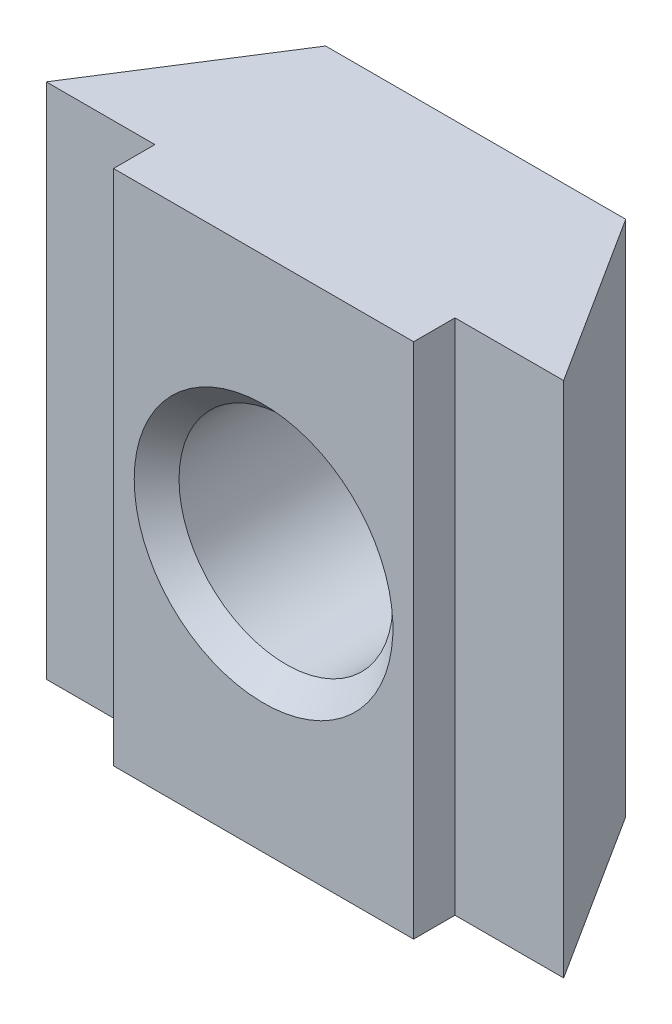
SolidWorks part; units mm, degrees
ref_plane "Piano frontale" through (0, 0, 0) normal (0, 0, 1) x (1, 0, 0)
ref_plane "Piano superiore" through (0, 0, 0) normal (0, 1, 0) x (1, 0, 0)
ref_plane "Piano destro" through (0, 0, 0) normal (1, 0, 0) x (0, 0, -1)
ref_plane "Plane1" through (0, 23.4, 0) normal (0, -1, 0) x (1, 0, 0)
sketch "Sketch1" plane through (0, 23.4, 0) normal (0, -1, 0) x (1, 0, 0)
  line L0 (-13.1, -10.8) -> (-11, -7.5)
  line L1 (-11, -7.5) -> (-21, -7.5)
  line L2 (-21, -7.5) -> (-18.9, -10.8)
  line L3 (-18.9, -10.8) -> (-13.1, -10.8)
extrude "Extrude1" add sketch "Sketch1" against normal blind 10
sketch "Sketch2" plane through (0, 0, -7.5) normal (0, 0, 1) x (1, 0, 0)
  line L0 (-18.9, 33.4) -> (-13.1, 33.4)
  line L1 (-13.1, 33.4) -> (-13.1, 23.4)
  line L2 (-13.1, 23.4) -> (-18.9, 23.4)
  line L3 (-18.9, 23.4) -> (-18.9, 33.4)
extrude "Extrude2" add sketch "Sketch2" along normal blind 0.8
hole_wizard "HoleWzd1" positions "Sketch4" profile "Sketch3" hole size "M3.5" standard "Ansi Metric"
sketch "Sketch4" plane through (0, 0, -6.7) normal (0, 0, 1) x (1, 0, 0)
  point P0 (-16, 28.4)
sketch "Sketch3" plane through (-16, 28.4, -6.7) normal (1, 0, 0) x (0, -1, 0)
  line L0 (0, 0) -> (0, 4.1)
  line L1 (0, 4.1) -> (2.067, 4.1)
  line L2 (2.067, 4.1) -> (2.067, 0)
  line L5 (2.067, 0) -> (0, 0)
  line L11 (0, -6.35) -> (0, 107.95) construction
  dimension "Thru Hole Dia." = 4.134
  dimension "Thru Hole Depth" = 4.1
chamfer "Chamfer1" distance 0.433 angle 45 2 edges at (-13.933, 28.4, -10.8) (-13.933, 28.4, -6.7)
